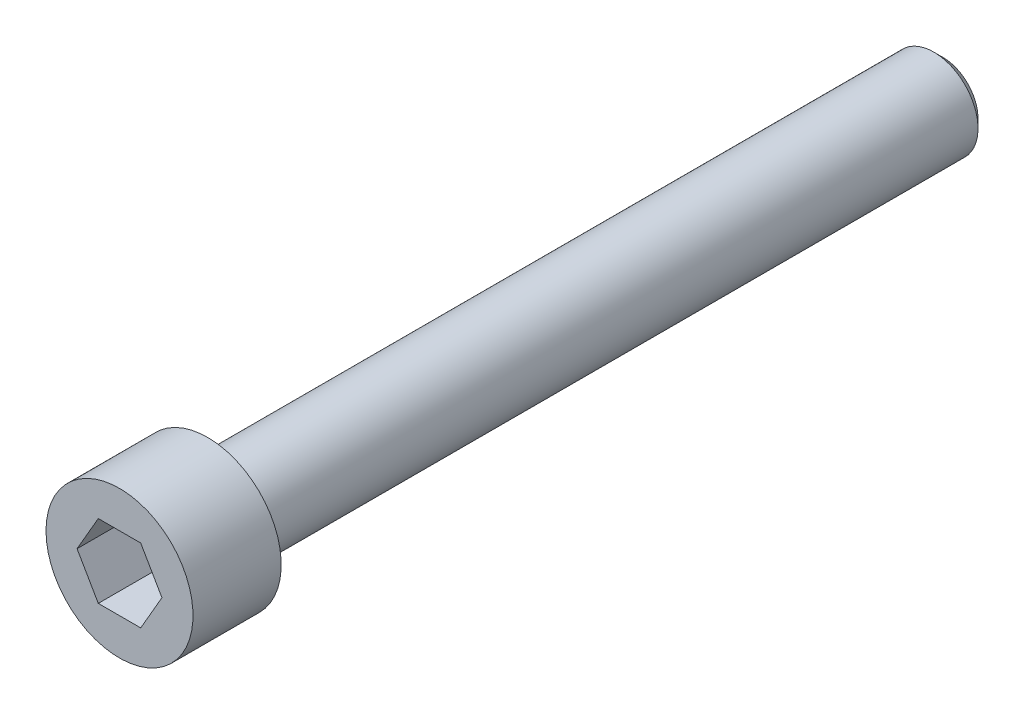
SolidWorks part; units mm, degrees
material "Простая углеродистая сталь"
ref_plane "Спереди" through (0, 0, 0) normal (0, 0, 1) x (1, 0, 0)
ref_plane "Сверху" through (0, 0, 0) normal (0, 1, 0) x (1, 0, 0)
ref_plane "Справа" through (0, 0, 0) normal (1, 0, 0) x (0, 0, -1)
sketch "Эскиз1" plane through (0, 0, 0) normal (1, 0, 0) x (0, 0, -1)
  line L0 (0, 0) -> (0, 2.5)
  line L1 (0, 2.5) -> (3, 2.5)
  line L2 (3, 2.5) -> (3, 1.5)
  line L3 (3, 1.5) -> (28, 1.5)
  line L4 (28, 1.5) -> (28, 0)
  line L5 (28, 0) -> (0, 0)
  line L6 (0, 0) -> (-1.7761, 0) construction
  dimension "D1" = 5
  dimension "D2" = 3
  dimension "D3" = 25
  dimension "D4" = 3
revolve "Повернуть1" add sketch "Эскиз1" angle 360 about L6
sketch "Эскиз2" plane through (0, 0, 0) normal (0, 0, 1) x (1, 0, 0)
  line L0 (0, 0) -> (0.8127, 0) construction
  line L1 (1.4434, 0) -> (0.7217, 1.25)
  line L2 (0.7217, 1.25) -> (-0.7217, 1.25)
  line L3 (-0.7217, 1.25) -> (-1.4434, 0)
  line L4 (-1.4434, 0) -> (-0.7217, -1.25)
  line L5 (-0.7217, -1.25) -> (0.7217, -1.25)
  line L6 (0.7217, -1.25) -> (1.4434, 0)
  circle A0 centre (0, 0) radius 1.25 construction
  dimension "D1" = 2.5
  dimension "D2" = 60
extrude "Вырез-Вытянуть1" cut sketch "Эскиз2" against normal blind 2
fillet "Скругление1" radius 0.3 1 edges at (-1.5, 0, -3)
chamfer "Фаска1" distance 0.3 angle 45 1 edges at (-1.5, 0, -28)
